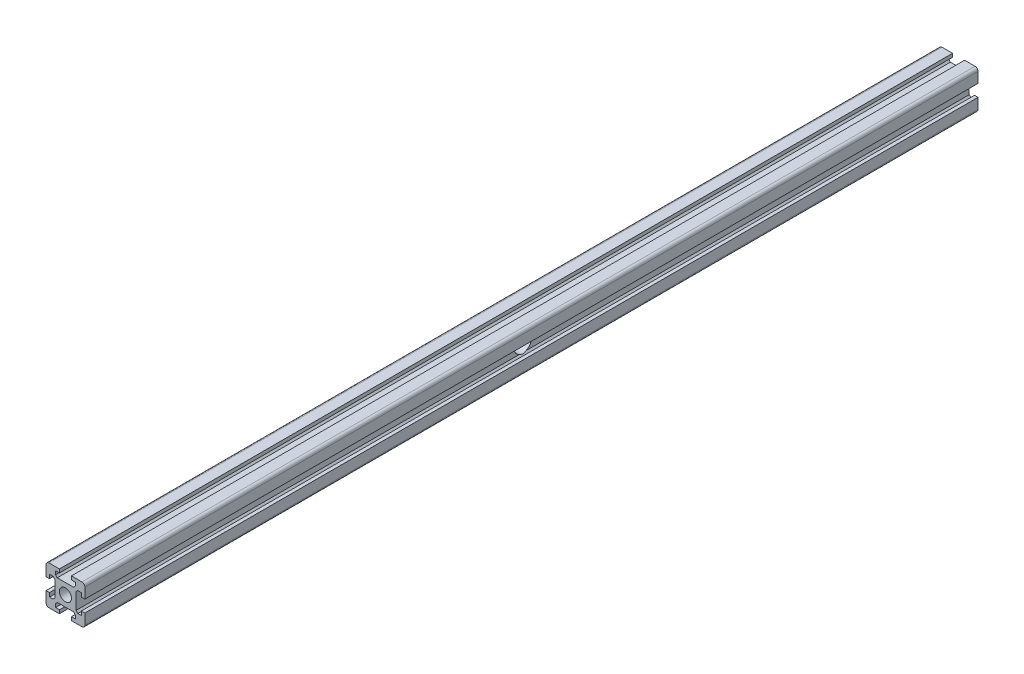
SolidWorks part; units mm, degrees
material "6061 Alloy"
ref_plane "Front Plane" through (0, 0, 0) normal (0, 0, 1) x (1, 0, 0)
ref_plane "Top Plane" through (0, 0, 0) normal (0, 1, 0) x (1, 0, 0)
ref_plane "Right Plane" through (0, 0, 0) normal (1, 0, 0) x (0, 0, -1)
sketch "Sketch1" plane through (0, 0, 0) normal (0, 0, 1) x (1, 0, 0)
  line L0 (-10, 3.1) -> (-8.2, 3.1)
  line L1 (-8.5, 10) -> (-3.1, 10) construction
  line L2 (-10, 8.5) -> (-10, 3.1) construction
  line L3 (-10, -3.1) -> (-10, -8.5) construction
  line L4 (-8.5, -10) -> (-3.1, -10) construction
  line L5 (-10, -3.1) -> (-10, -8.5)
  line L6 (-8.5, -10) -> (-3.1, -10)
  line L7 (-8.2, 3.1) -> (-8.2, 5.1)
  line L8 (-8.2, 5.1) -> (-6.4, 5.1)
  line L9 (-10, -3.1) -> (-8.2, -3.1)
  line L10 (-8.2, -3.1) -> (-8.2, -5.1)
  line L11 (-8.2, -5.1) -> (-6.4, -5.1)
  line L13 (-6.4, 5.1) -> (-5.4929, 4.1929)
  line L14 (-5.4929, 4.1929) -> (-5.4929, -4.1929)
  line L15 (-6.4, -5.1) -> (-5.4929, -4.1929)
  line L16 (-3.1, 10) -> (-3.1, 8.2)
  line L17 (-3.1, 8.2) -> (-5.1, 8.2)
  line L19 (-5.1, 8.2) -> (-5.1, 6.4)
  line L20 (-5.1, 6.4) -> (-4.1929, 5.4929)
  line L21 (-4.1929, 5.4929) -> (4.1929, 5.4929)
  line L22 (4.1929, 5.4929) -> (5.1, 6.4)
  line L23 (5.1, 6.4) -> (5.1, 8.2)
  line L24 (5.1, 8.2) -> (3.1, 8.2)
  line L25 (3.1, 8.2) -> (3.1, 10)
  line L26 (-3.1, -10) -> (-3.1, -8.2)
  line L27 (-3.1, -8.2) -> (-5.1, -8.2)
  line L28 (-5.1, -8.2) -> (-5.1, -6.4)
  line L29 (-5.1, -6.4) -> (-4.1929, -5.4929)
  line L30 (-4.1929, -5.4929) -> (4.1929, -5.4929)
  line L31 (4.1929, -5.4929) -> (5.1, -6.4)
  line L32 (5.1, -6.4) -> (5.1, -8.2)
  line L33 (5.1, -8.2) -> (3.1, -8.2)
  line L34 (3.1, -8.2) -> (3.1, -10)
  line L35 (3.1, -10) -> (8.5, -10)
  line L36 (10, -8.5) -> (10, -3.1)
  line L37 (10, -3.1) -> (8.2, -3.1)
  line L38 (8.2, -3.1) -> (8.2, -5.1)
  line L39 (8.2, -5.1) -> (6.4, -5.1)
  line L40 (6.4, -5.1) -> (5.4929, -4.1929)
  line L41 (5.4929, -4.1929) -> (5.4929, 4.1929)
  line L42 (5.4929, 4.1929) -> (6.4, 5.1)
  line L43 (6.4, 5.1) -> (8.2, 5.1)
  line L44 (8.2, 5.1) -> (8.2, 3.1)
  line L45 (8.2, 3.1) -> (10, 3.1)
  line L46 (10, 3.1) -> (10, 8.5)
  line L47 (8.5, 10) -> (3.1, 10)
  line L48 (-3.1, 10) -> (-8.5, 10)
  line L49 (-10, 8.5) -> (-10, 3.1)
  arc A0 (-8.5, 10) -> (-10, 8.5) centre (-8.5, 8.5) ccw
  arc A1 (-10, -8.5) -> (-8.5, -10) centre (-8.5, -8.5) ccw construction
  arc A2 (8.5, -10) -> (10, -8.5) centre (8.5, -8.5) ccw
  arc A3 (8.5, 10) -> (10, 8.5) centre (8.5, 8.5) cw
  arc A4 (-8.5, -10) -> (-10, -8.5) centre (-8.5, -8.5) cw
  circle A6 centre (0, 0) radius 3.1
  point P0 (0, 0)
  point P44 (-5.2, -3.4858)
  point P47 (-5.2, 3.4858)
  dimension "D3" = 5.4929
  dimension "D5" = 1.5
  dimension "D1" = 6.2
  dimension "D2" = 5.4929
  dimension "D4" = 1.5
  dimension "D6" = 1.5
extrude "Boss-Extrude1" add sketch "Sketch1" along normal blind 460
sketch "Sketch5" plane through (-5.4929, 0, 0) normal (-1, 0, 0) x (0, 0, -1)
  line L2 (-460, 10) -> (0, 10) construction
  circle A0 centre (-230, 0) radius 4.5
  dimension "D1" = 9
  dimension "D2" = 230
  dimension "D3" = 10
extrude "Cut-Extrude2" cut sketch "Sketch5" against normal blind 12 and the other way through all
